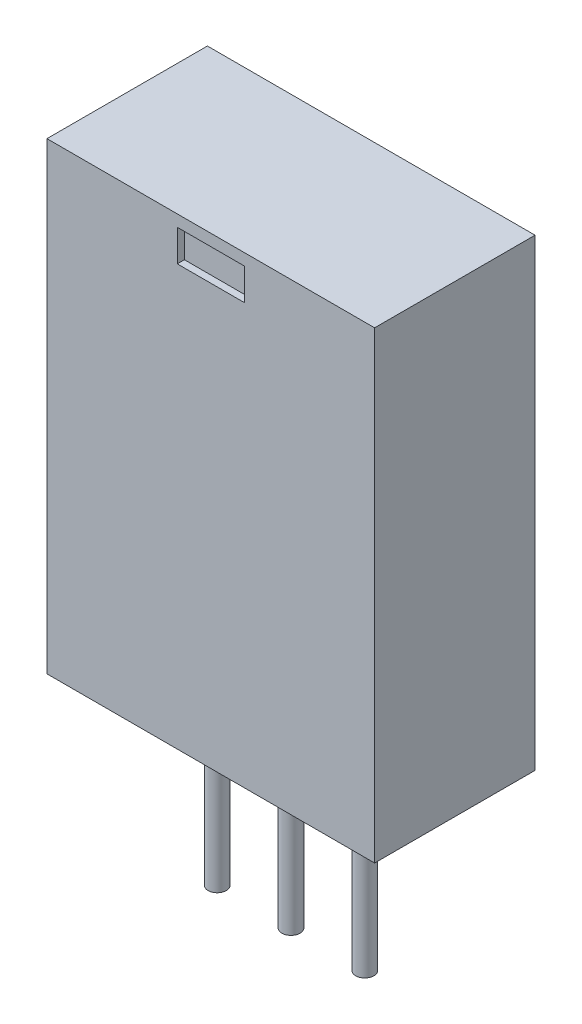
SolidWorks part; units mm, degrees
ref_plane "Front Plane" through (0, 0, 0) normal (0, 0, 1) x (1, 0, 0)
ref_plane "Top Plane" through (0, 0, 0) normal (0, 1, 0) x (1, 0, 0)
ref_plane "Right Plane" through (0, 0, 0) normal (1, 0, 0) x (0, 0, -1)
sketch "Sketch1" plane through (0, 0, 0) normal (0, 0, 1) x (1, 0, 0)
  line L1 (-5.8357, -8.255) -> (5.8356, -8.255)
  line L2 (-5.8357, -8.255) -> (-5.8357, 8.255)
  line L3 (-5.8357, 8.255) -> (5.8356, 8.255)
  line L4 (5.8356, -8.255) -> (5.8356, 8.255)
  line L5 (-5.8357, -8.255) -> (5.8356, 8.255) construction
  line L6 (-5.8357, 8.255) -> (5.8356, -8.255) construction
  point P0 (0, 0)
  dimension "D1" = 11.6713
  dimension "D2" = 16.51
extrude "Boss-Extrude1" add sketch "Sketch1" along normal blind 5.715
sketch "Sketch2" plane through (0, 0, 5.715) normal (0, 0, 1) x (1, 0, 0)
  line L1 (-1.1925, 7.8417) -> (1.1925, 7.8417)
  line L2 (-1.1925, 7.8417) -> (-1.1925, 6.7133)
  line L3 (-1.1925, 6.7133) -> (1.1925, 6.7133)
  line L4 (1.1925, 7.8417) -> (1.1925, 6.7133)
  line L5 (-1.1925, 7.8417) -> (1.1925, 6.7133) construction
  line L6 (-1.1925, 6.7133) -> (1.1925, 7.8417) construction
  point P0 (0, 7.2775)
extrude "Cut-Extrude1" cut sketch "Sketch2" against normal blind 0.254
sketch "Sketch3" plane through (0, -8.255, 0) normal (0, -1, 0) x (1, 0, 0)
  line L0 (-5.8357, 2.8575) -> (5.8356, 2.8575) construction
  line L1 (-5.8357, 5.715) -> (-5.8357, 0) construction
  line L2 (5.8356, 5.715) -> (5.8356, 0) construction
  circle A0 centre (-2.6289, 2.8575) radius 0.3238
  circle A1 centre (0, 2.8575) radius 0.3238
  circle A2 centre (2.6289, 2.8575) radius 0.3238
  dimension "D1" = 0.6477
  dimension "D4" = 2.6289
  dimension "D2" = 11.6713
  dimension "D3" = 2.6289
extrude "Boss-Extrude2" add sketch "Sketch3" along normal blind 6.35
equation "\"D3@Sketch3\"=\"D4@Sketch3\""
